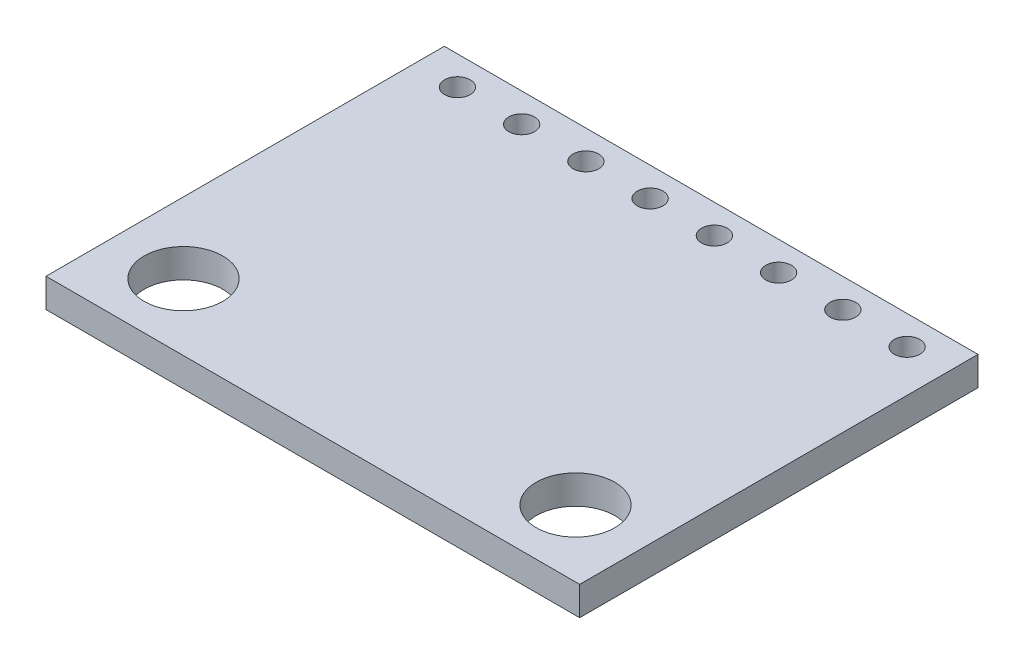
SolidWorks part; units mm, degrees
material "Silicon"
ref_plane "Front Plane" through (0, 0, 0) normal (0, 0, 1) x (1, 0, 0)
ref_plane "Top Plane" through (0, 0, 0) normal (0, 1, 0) x (1, 0, 0)
ref_plane "Right Plane" through (0, 0, 0) normal (1, 0, 0) x (0, 0, -1)
sketch "Sketch1" plane through (0, 0, 0) normal (0, 1, 0) x (1, 0, 0)
  line L0 (0, 0) -> (0, 4.6714) construction
  line L1 (-10.55, -7.874) -> (10.55, -7.874)
  line L2 (-10.55, -7.874) -> (-10.55, 7.874)
  line L3 (-10.55, 7.874) -> (10.55, 7.874)
  line L4 (10.55, -7.874) -> (10.55, 7.874)
  line L5 (-10.55, -7.874) -> (10.55, 7.874) construction
  line L6 (-10.55, 7.874) -> (10.55, -7.874) construction
  circle A0 centre (-7.75, -5.2388) radius 1.5557
  circle A1 centre (7.75, -5.2388) radius 1.5558
  circle A2 centre (-8.89, 6.731) radius 0.508
  circle A3 centre (-6.35, 6.731) radius 0.508
  circle A4 centre (-3.81, 6.731) radius 0.508
  circle A5 centre (-1.27, 6.731) radius 0.508
  circle A6 centre (1.27, 6.731) radius 0.508
  circle A7 centre (3.81, 6.731) radius 0.508
  circle A8 centre (6.35, 6.731) radius 0.508
  circle A9 centre (8.89, 6.731) radius 0.508
  point P0 (0, 0)
  dimension "D3" = 3.1115
  dimension "D7" = 1.016
  dimension "D10" = 2.8
  dimension "D4" = 15.5
  dimension "D1" = 21.1
  dimension "D2" = 15.748
  dimension "D5" = 2.6353
  dimension "D6" = 1.66
  dimension "D8" = 1.143
  dimension "D9" = 8
extrude "Boss-Extrude1" add sketch "Sketch1" along normal mid plane 1.143
